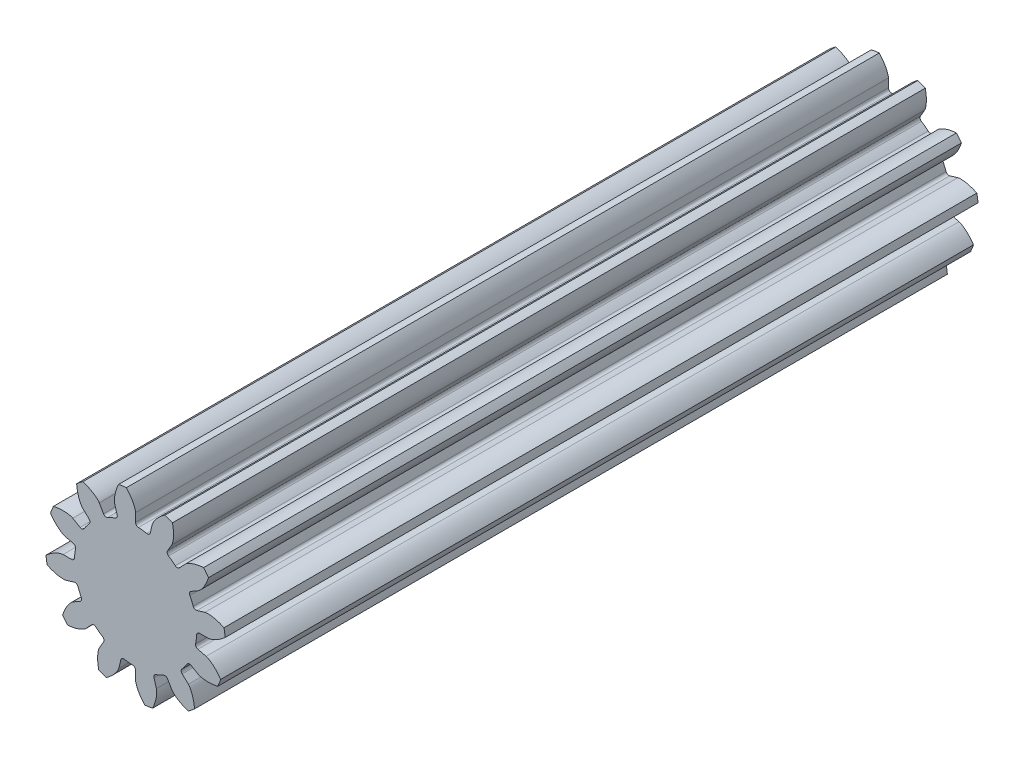
SolidWorks part; units mm, degrees
ref_plane "Front Plane" through (0, 0, 0) normal (0, 0, 1) x (1, 0, 0)
ref_plane "Top Plane" through (0, 0, 0) normal (0, 1, 0) x (1, 0, 0)
ref_plane "Right Plane" through (0, 0, 0) normal (1, 0, 0) x (0, 0, -1)
sketch "Sketch1" plane through (0, 0, 0) normal (0, 0, 1) x (1, 0, 0)
  circle A0 centre (0, 0) radius 3.0374
  dimension "D1" = 6.0748
extrude "Boss-Extrude1" add sketch "Sketch1" against normal blind 25.4
sketch "Sketch2" plane through (0, 0, 0) normal (0, 0, 1) x (1, 0, 0)
  line L0 (2.0611, 0) -> (2.4465, 0)
  line L1 (0, 0) -> (3.017, -0.3515) construction
  line L2 (2.0059, -0.4739) -> (2.381, -0.5625)
  circle A0 centre (0, 0) radius 2.6035 construction
  circle A1 centre (0, 0) radius 2.4465 construction
  arc A2 (2.0059, -0.4739) -> (2.0611, 0) centre (0, 0) ccw
  circle A3 centre (0, 0) radius 3.0374 construction
  spline S0 degree 4 poles (2.4465, 0) (2.4483, 0) (2.4534, 0.0003) (2.4629, 0.0012) (2.4785, 0.0033) (2.4981, 0.007) (2.5234, 0.0128) (2.5529, 0.0211) (2.5849, 0.0317) (2.6193, 0.0448) (2.6532, 0.0592) (2.6865, 0.0748) (2.7193, 0.0915) (2.7585, 0.1131) (2.8047, 0.1407) (2.8575, 0.1756) (2.9157, 0.2181) (2.9733, 0.2645) (3.0284, 0.3127) (3.0822, 0.3642) (3.1328, 0.4159) (3.1834, 0.4723) (3.2289, 0.5258) (3.2774, 0.5886) (3.3159, 0.64) (3.3639, 0.7108) (3.3914, 0.7534) (3.4226, 0.8042) (3.4359, 0.8273) (3.4441, 0.8415) knots 0 0 0 0 0 0.005377 0.015084 0.028532 0.04661 0.064855 0.092111 0.119476 0.146842 0.174209 0.201575 0.228941 0.256307 0.307035 0.361767 0.4165 0.471232 0.525964 0.580697 0.635429 0.690161 0.744894 0.799626 0.854358 0.909091 0.954545 1 1 1 1 1 construction
  spline S1 degree 4 poles (2.4465, 0) (2.4483, 0) (2.4534, 0.0003) (2.4629, 0.0012) (2.4785, 0.0033) (2.4981, 0.007) (2.5234, 0.0128) (2.5529, 0.0211) (2.5849, 0.0317) (2.6193, 0.0448) (2.6532, 0.0592) (2.6865, 0.0748) (2.7193, 0.0915) (2.7585, 0.1131) (2.8047, 0.1407) (2.8575, 0.1756) (2.9157, 0.2181) (2.9733, 0.2645) (3.0284, 0.3127) (3.0822, 0.3642) (3.1328, 0.4159) (3.1834, 0.4723) (3.2289, 0.5258) (3.2774, 0.5886) (3.3159, 0.64) (3.3535, 0.6954) (3.3715, 0.7227) (3.3805, 0.7368) knots 0 0 0 0 0 0.005377 0.015084 0.028532 0.04661 0.064855 0.092111 0.119476 0.146842 0.174209 0.201575 0.228941 0.256307 0.307035 0.361767 0.4165 0.471232 0.525964 0.580697 0.635429 0.690161 0.744894 0.799626 0.854358 0.909091 0.909091 0.909091 0.909091 0.909091
  spline S2 degree 4 poles (2.381, -0.5625) (2.3827, -0.5629) (2.3876, -0.5643) (2.3967, -0.5674) (2.4113, -0.573) (2.4296, -0.5811) (2.4529, -0.5926) (2.4796, -0.6075) (2.5083, -0.6251) (2.5388, -0.6458) (2.5685, -0.6676) (2.5973, -0.6905) (2.6254, -0.7143) (2.6586, -0.7443) (2.6972, -0.7818) (2.7406, -0.8278) (2.7875, -0.8826) (2.8328, -0.941) (2.8754, -1.0006) (2.9159, -1.0631) (2.9533, -1.1251) (2.9895, -1.1916) (3.0215, -1.2541) (3.0543, -1.3263) (3.0799, -1.3852) (3.1104, -1.4651) (3.1273, -1.5129) (3.146, -1.5696) (3.1537, -1.5951) (3.1584, -1.6108) knots 0 0 0 0 0 0.005377 0.015084 0.028532 0.04661 0.064855 0.092111 0.119476 0.146842 0.174209 0.201575 0.228941 0.256307 0.307035 0.361767 0.4165 0.471232 0.525964 0.580697 0.635429 0.690161 0.744894 0.799626 0.854358 0.909091 0.954545 1 1 1 1 1 construction
  spline S3 degree 4 poles (2.381, -0.5625) (2.3827, -0.5629) (2.3876, -0.5643) (2.3967, -0.5674) (2.4113, -0.573) (2.4296, -0.5811) (2.4529, -0.5926) (2.4796, -0.6075) (2.5083, -0.6251) (2.5388, -0.6458) (2.5685, -0.6676) (2.5973, -0.6905) (2.6254, -0.7143) (2.6586, -0.7443) (2.6972, -0.7818) (2.7406, -0.8278) (2.7875, -0.8826) (2.8328, -0.941) (2.8754, -1.0006) (2.9159, -1.0631) (2.9533, -1.1251) (2.9895, -1.1916) (3.0215, -1.2541) (3.0543, -1.3263) (3.0799, -1.3852) (3.1038, -1.4478) (3.115, -1.4785) (3.1205, -1.4943) knots 0 0 0 0 0 0.005377 0.015084 0.028532 0.04661 0.064855 0.092111 0.119476 0.146842 0.174209 0.201575 0.228941 0.256307 0.307035 0.361767 0.4165 0.471232 0.525964 0.580697 0.635429 0.690161 0.744894 0.799626 0.854358 0.909091 0.909091 0.909091 0.909091 0.909091
  dimension "D1" = 5.207
  dimension "D2" = 4.893
  dimension "D3" = 4.1222
  dimension "D4" = 6.646
  dimension "D5" = 6.646
extrude "Cut-Extrude1" cut sketch "Sketch2" against normal through all and the other way through all
fillet "Fillet1" radius 0.1016 2 edges at (2.0611, 0, -12.7) (2.0059, -0.4739, -12.7)
pattern_circular "CirPattern1" count 12 over 360 about axis through (0, 0, -25.4) along (0, 0, 1) of "Cut-Extrude1", "Fillet1"
equation "\"P\"= 58.53658'Diameral Pitch"
equation "\"N\"= 12'Number of Teeth"
equation "\"phi\"= 20deg'Pressure Angle"
equation "\"a\"= 1 / \"P\"'Addendum"
equation "\"b\"= 1.25 / \"P\"'Dedendum"
equation "\"c\"= \"b\" - \"a\"'Clearence"
equation "\"dp\"= \"N\" / \"P\"'Pitch Circle Diameter"
equation "\"db\"= \"dp\" * cos ( \"phi\" )'Base Circle Diameter"
equation "\"D1@Sketch1\"= \"dp\" + 2 * \"a\"'Addendum Circle Diameter"
equation "\"D1@Sketch2\"= \"dp\"'Pitch Circle Diameter"
equation "\"D2@Sketch2\"= \"db\"'Base Circle Diameter"
equation "\"D3@Sketch2\"= \"dp\" - 2 * \"b\"'Dedendum Circle Diameter"
equation "\"alpha\"= sqr ( \"dp\" ^ 2 - \"db\" ^ 2 ) / \"db\" * 180 / pi - \"phi\""
equation "\"D4@Sketch2\"= 360 / ( 4 * \"N\" ) - \"alpha\""
equation "\"D5@Sketch2\"= 360 / ( 4 * \"N\" ) - \"alpha\""
